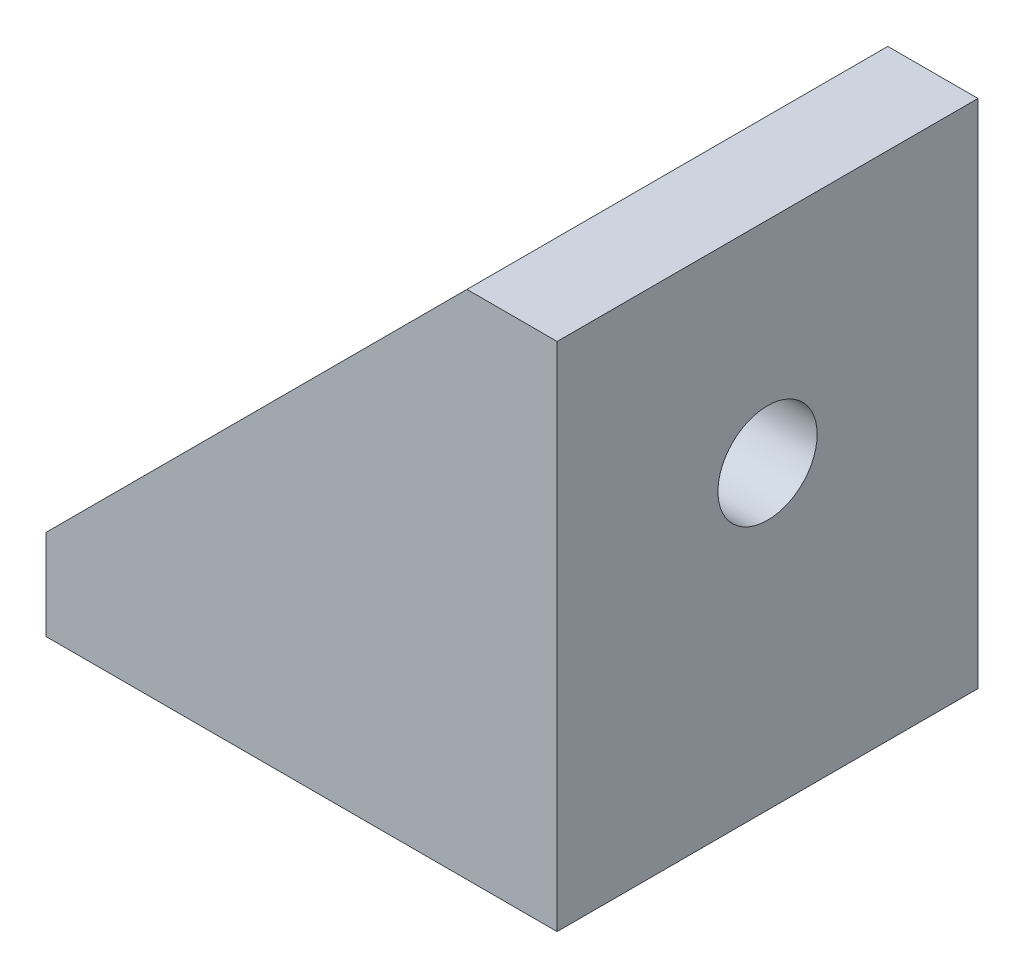
SolidWorks part; units mm, degrees
ref_plane "Front Plane" through (0, 0, 0) normal (0, 0, 1) x (1, 0, 0)
ref_plane "Top Plane" through (0, 0, 0) normal (0, 1, 0) x (1, 0, 0)
ref_plane "Right Plane" through (0, 0, 0) normal (1, 0, 0) x (0, 0, -1)
sketch "Sketch1" plane through (0, 0, 0) normal (0, 1, 0) x (1, 0, 0)
  line L0 (0, 0) -> (-14, 0)
  line L1 (-14, 0) -> (-14, 14)
  line L2 (-14, 14) -> (0, 14)
  line L3 (0, 14) -> (0, 0)
  line L4 (0, 14) -> (-14, 0) construction
  circle A3 centre (-7, 7) radius 1.75
  dimension "D1" = 3.5
  dimension "D2" = 14
  dimension "D3" = 14
extrude "Boss-Extrude1" add sketch "Sketch1" along normal blind 3
sketch "Sketch2" plane through (0, 0, 0) normal (1, 0, 0) x (0, 0, -1)
  line L0 (0, 3) -> (14, 17) construction
  line L1 (0, 0) -> (14, 0)
  line L2 (0, 0) -> (0, 17)
  line L3 (0, 17) -> (14, 17)
  line L4 (14, 0) -> (14, 17)
  line L5 (14, 3) -> (14, 0) construction
  line L6 (0, 0) -> (14, 0) construction
  circle A0 centre (7, 10) radius 1.65
  dimension "D2" = 3.3
  dimension "D1" = 17
extrude "Boss-Extrude2" add sketch "Sketch2" along normal blind 3
sketch "Sketch3" plane through (0, 0, 0) normal (0, 0, 1) x (1, 0, 0)
  line L0 (0, 3) -> (0, 17)
  line L1 (0, 17) -> (-14, 3)
  line L2 (-14, 3) -> (0, 3)
extrude "Boss-Extrude3" add sketch "Sketch3" against normal blind 2
sketch "Sketch4" plane through (0, 0, -14) normal (0, 0, -1) x (-1, 0, 0)
  line L0 (0, 3) -> (14, 3)
  line L1 (14, 3) -> (0, 17)
  line L2 (0, 17) -> (0, 3)
extrude "Boss-Extrude4" add sketch "Sketch4" against normal blind 2
